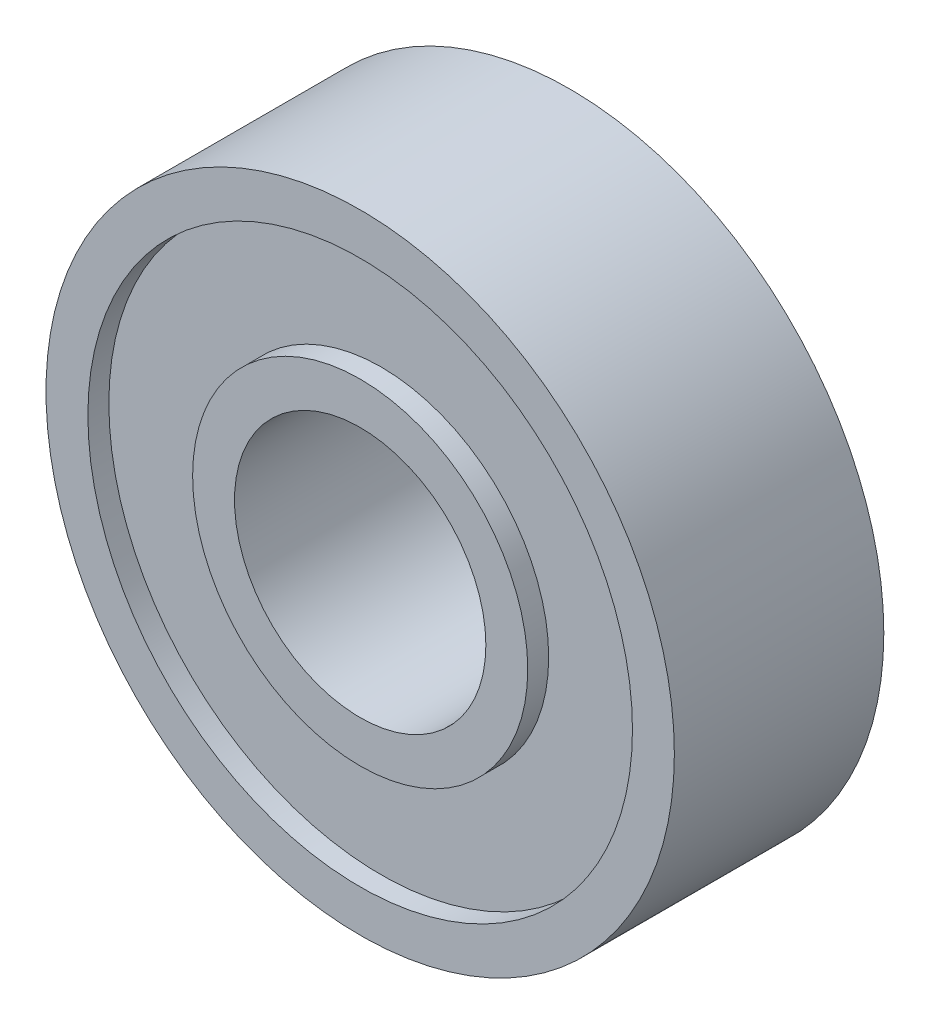
SolidWorks part; units mm, degrees
ref_plane "Front" through (0, 0, 0) normal (0, 0, 1) x (1, 0, 0)
ref_plane "Top" through (0, 0, 0) normal (0, 1, 0) x (1, 0, 0)
ref_plane "Right" through (0, 0, 0) normal (1, 0, 0) x (0, 0, -1)
sketch "Esquisse1" plane through (0, 0, 0) normal (0, 0, 1) x (1, 0, 0)
  circle A0 centre (0, 0) radius 7.5
  circle A1 centre (0, 0) radius 3
  dimension "D1" = 6
  dimension "D2" = 15
extrude "Boss.-Extru.1" add sketch "Esquisse1" along normal blind 5
sketch "Esquisse2" plane through (0, 0, 5) normal (0, 0, 1) x (1, 0, 0)
  circle A0 centre (0, 0) radius 4
  circle A1 centre (0, 0) radius 6.5
  circle A2 centre (0, 0) radius 7.5 construction
  circle A3 centre (0, 0) radius 3 construction
  dimension "D1" = 1
  dimension "D2" = 1
extrude "Enlèv. mat.-Extru.1" cut sketch "Esquisse2" against normal blind 0.5
ref_plane "Plan2" through (0, 0, 2.5) normal (0, 0, -1) x (-1, 0, 0)
mirror "Symétrie2" about plane through (0, 0, 2.5) normal (0, 0, -1) of "Enlèv. mat.-Extru.1"
